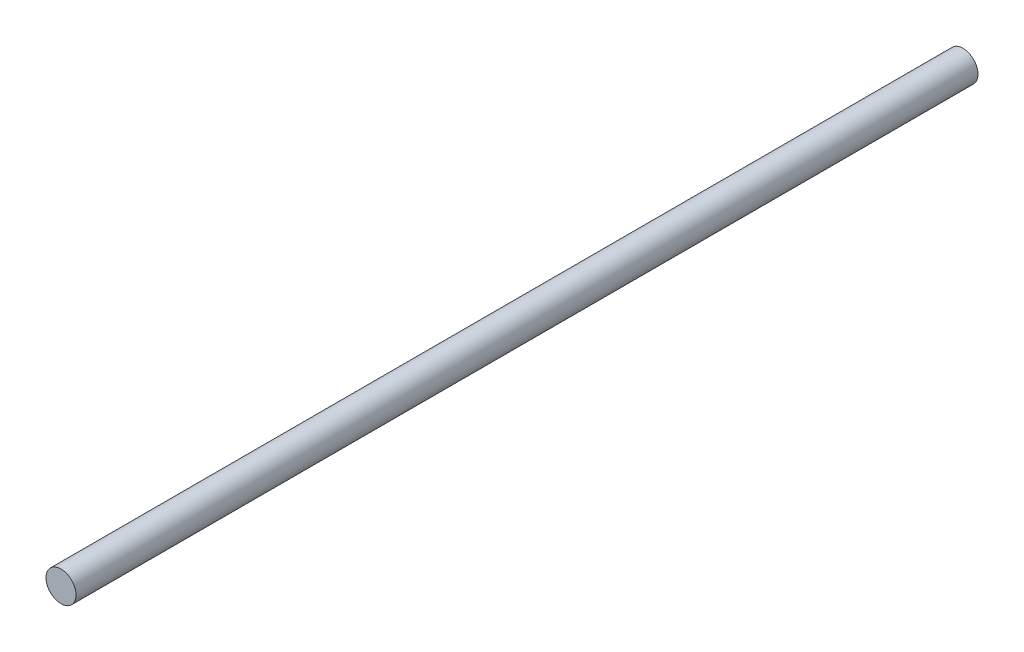
SolidWorks part; units mm, degrees
ref_plane "Front Plane" through (0, 0, 0) normal (0, 0, 1) x (1, 0, 0)
ref_plane "Top Plane" through (0, 0, 0) normal (0, 1, 0) x (1, 0, 0)
ref_plane "Right Plane" through (0, 0, 0) normal (1, 0, 0) x (0, 0, -1)
sketch "Sketch1" plane through (0, 0, 0) normal (0, 0, 1) x (1, 0, 0)
  circle A0 centre (0, 0) radius 10
  dimension "D1" = 20
extrude "Boss-Extrude1" add sketch "Sketch1" along normal blind 600
sketch "Sketch2" plane through (0, 0, 0) normal (0, 0, -1) x (-1, 0, 0)
  circle A0 centre (0, 0) radius 5
  dimension "D1" = 10
extrude "Cut-Extrude1" cut sketch "Sketch2" against normal blind 150
